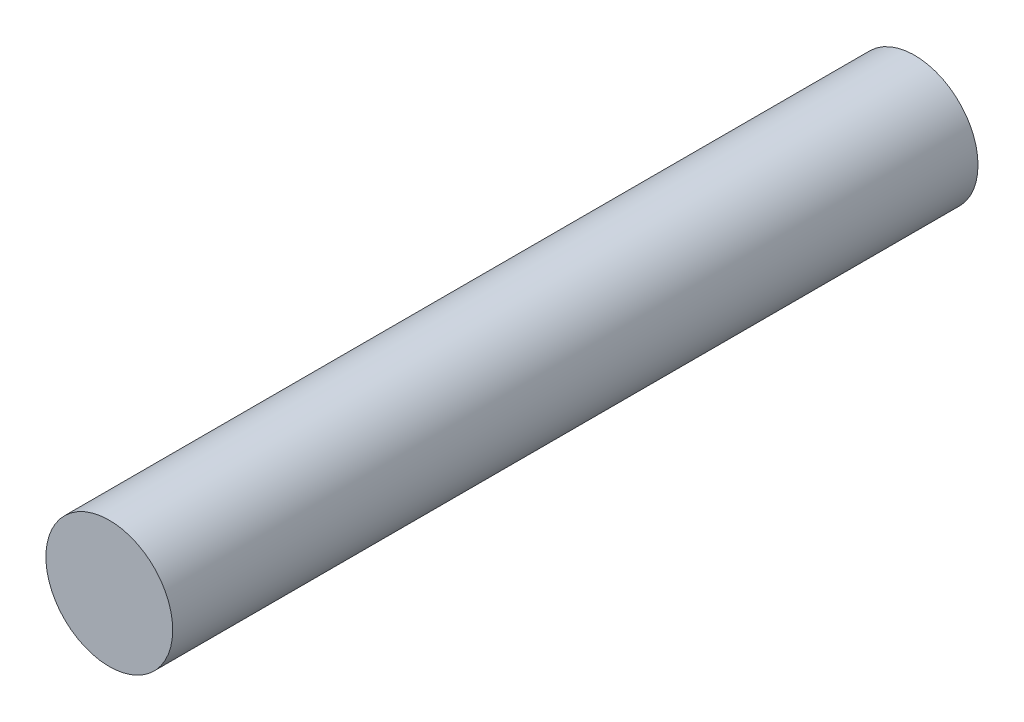
SolidWorks part; units mm, degrees
ref_plane "Front Plane" through (0, 0, 0) normal (0, 0, 1) x (1, 0, 0)
ref_plane "Top Plane" through (0, 0, 0) normal (0, 1, 0) x (1, 0, 0)
ref_plane "Right Plane" through (0, 0, 0) normal (1, 0, 0) x (0, 0, -1)
sketch "Sketch1" plane through (0, 0, 0) normal (0, 0, 1) x (1, 0, 0)
  circle A0 centre (0, 0) radius 4
  dimension "D1" = 8
extrude "Boss-Extrude1" add sketch "Sketch1" along normal blind 50.8
